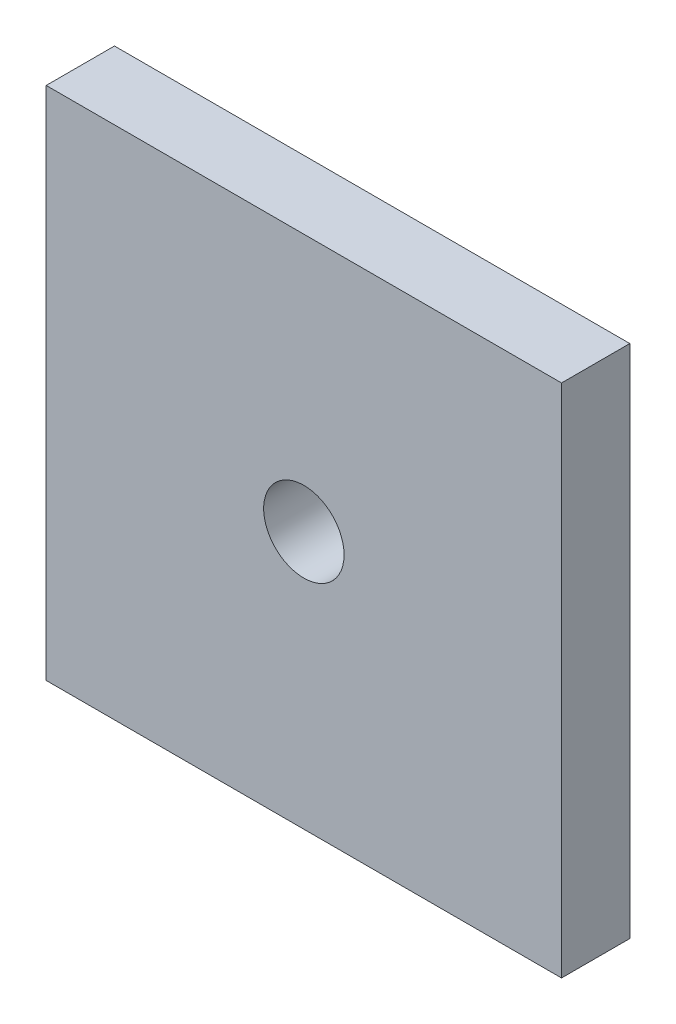
SolidWorks part; units mm, degrees
ref_plane "Front Plane" through (0, 0, 0) normal (0, 0, 1) x (1, 0, 0)
ref_plane "Top Plane" through (0, 0, 0) normal (0, 1, 0) x (1, 0, 0)
ref_plane "Right Plane" through (0, 0, 0) normal (1, 0, 0) x (0, 0, -1)
sketch "Sketch2" plane through (0, 0, 0) normal (0, 0, 1) x (1, 0, 0)
  line L1 (-25.4, -25.4) -> (25.4, -25.4)
  line L2 (-25.4, -25.4) -> (-25.4, 25.4)
  line L3 (-25.4, 25.4) -> (25.4, 25.4)
  line L4 (25.4, -25.4) -> (25.4, 25.4)
  line L5 (-25.4, -25.4) -> (25.4, 25.4) construction
  line L6 (-25.4, 25.4) -> (25.4, -25.4) construction
  circle A0 centre (0, 0) radius 3.9624
  point P0 (0, 0)
  dimension "ID" = 7.9248
  dimension "WD" = 50.8
  dimension "LG" = 50.8
extrude "Boss-Extrude1" add sketch "Sketch2" along normal blind 6.731
